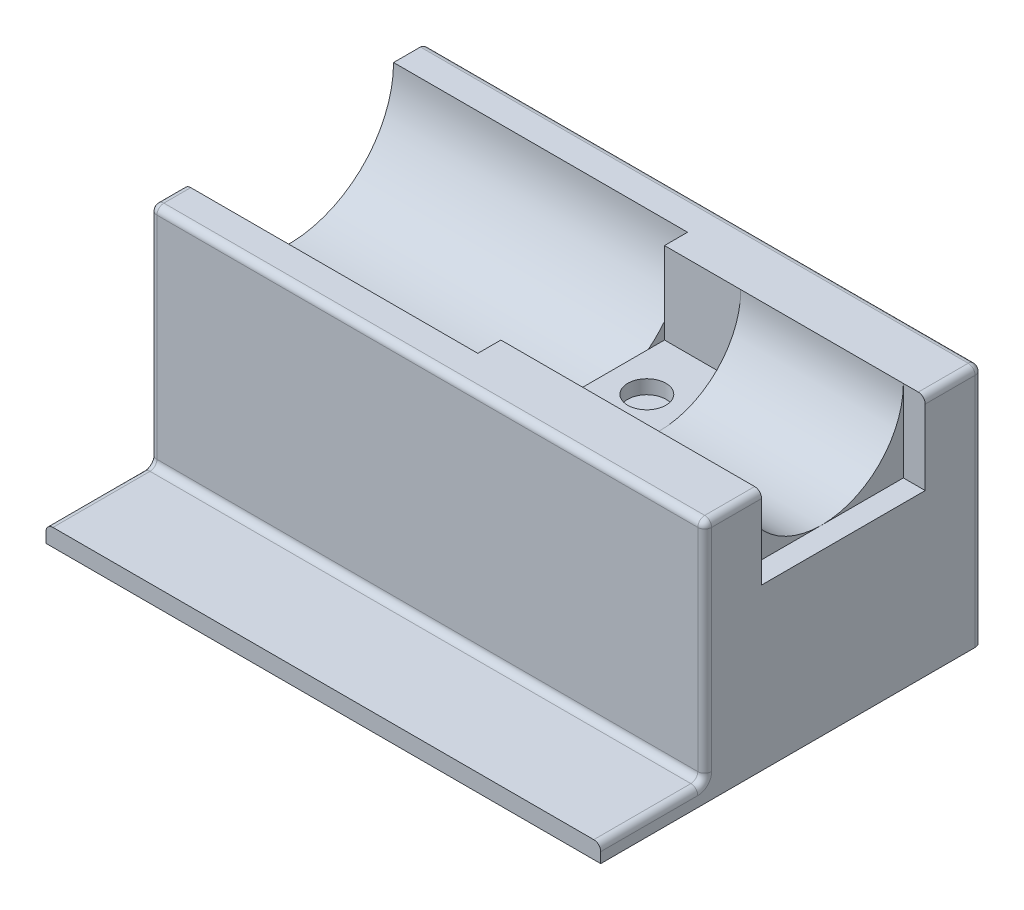
SolidWorks part; units mm, degrees
material "ABS"
ref_plane "Front Plane" through (0, 0, 0) normal (0, 0, 1) x (1, 0, 0)
ref_plane "Top Plane" through (0, 0, 0) normal (0, 1, 0) x (1, 0, 0)
ref_plane "Right Plane" through (0, 0, 0) normal (1, 0, 0) x (0, 0, -1)
sketch "Sketch1" plane through (0, 0, 0) normal (0, 1, 0) x (1, 0, 0)
  line L1 (0, 0) -> (203.2, 0)
  line L2 (0, 0) -> (0, -101.6)
  line L3 (0, -101.6) -> (203.2, -101.6)
  line L4 (203.2, 0) -> (203.2, -101.6)
  dimension "D1" = 101.6
  dimension "D2" = 203.2
extrude "Boss-Extrude1" add sketch "Sketch1" along normal blind 88.9
sketch "Sketch2" plane through (203.2, 0, 0) normal (1, 0, 0) x (0, 0, -1)
  line L0 (-101.6, 88.9) -> (0, 88.9) construction
  circle A0 centre (-50.8, 88.9) radius 29.972
  dimension "D2" = 59.944
  dimension "D1" = 50.8
extrude "Cut-Extrude1" cut sketch "Sketch2" against normal blind 203.2
sketch "Sketch3" plane through (203.2, 0, 0) normal (1, 0, 0) x (0, 0, -1)
  line L1 (-20.828, 118.872) -> (-80.772, 118.872)
  line L2 (-20.828, 118.872) -> (-20.828, 58.928)
  line L3 (-20.828, 58.928) -> (-80.772, 58.928)
  line L4 (-80.772, 118.872) -> (-80.772, 58.928)
  line L5 (-20.828, 118.872) -> (-80.772, 58.928) construction
  line L6 (-20.828, 58.928) -> (-80.772, 118.872) construction
  point P0 (-50.8, 88.9)
  dimension "D1" = 29.972
  dimension "D2" = 29.972
extrude "Cut-Extrude2" cut sketch "Sketch3" against normal blind 8.001
ref_plane "Plane1" through (135.636, 0, 0) normal (1, 0, 0) x (0, 0, -1)
sketch "Sketch4" plane through (135.636, 0, 0) normal (1, 0, 0) x (0, 0, -1)
  line L1 (-80.772, 58.928) -> (-20.828, 58.928)
  line L2 (-80.772, 58.928) -> (-80.772, 88.9)
  line L3 (-80.772, 88.9) -> (-20.828, 88.9)
  line L4 (-20.828, 58.928) -> (-20.828, 88.9)
extrude "Cut-Extrude3" cut sketch "Sketch4" against normal blind 27.94
sketch "Sketch5" plane through (0, 0, 0) normal (-1, 0, 0) x (0, 0, 1)
  line L0 (0, 88.9) -> (20.828, 88.9) construction
  circle A0 centre (50.8, 88.9) radius 38.4175
  dimension "D3" = 76.835
  dimension "D1" = 0
  dimension "D2" = 50.8
extrude "Cut-Extrude4" cut sketch "Sketch5" against normal blind 107.696
sketch "Sketch6" plane through (0, 58.928, 0) normal (0, 1, 0) x (1, 0, 0)
  line L0 (135.636, -50.8) -> (107.696, -50.8) construction
  line L1 (107.696, -74.833) -> (107.696, -26.767) construction
  line L2 (121.666, -50.8) -> (121.666, -31.75)
  circle A0 centre (121.666, -41.275) radius 6.985
  dimension "D2" = 13.97
  dimension "D1" = 19.05
extrude "Cut-Extrude5" cut sketch "Sketch6" against normal blind 5.08 contours L2 A0 | L2 A0
sketch "Sketch7" plane through (0, 0, 101.6) normal (0, 0, 1) x (1, 0, 0)
  line L0 (203.2, 88.9) -> (203.2, 0) construction
  line L1 (0, 0) -> (203.2, 0)
  line L2 (0, 0) -> (0, 6.35)
  line L3 (0, 6.35) -> (203.2, 6.35)
  line L4 (203.2, 0) -> (203.2, 6.35)
  dimension "D1" = 6.35
extrude "Boss-Extrude2" add sketch "Sketch7" along normal blind 38.1
fillet "Fillet1" radius 2.54 12 edges at (101.6, 6.35, 101.6) (0, 6.35, 120.65) (203.2, 6.35, 120.65) (0, 44.45, 0) (0, 88.9, 95.4087) (0, 47.625, 101.6) (101.6, 88.9, 0) (203.2, 44.45, 0) (203.2, 88.9, 10.414) (203.2, 88.9, 91.186) (101.6, 88.9, 101.6) (203.2, 47.625, 101.6)
